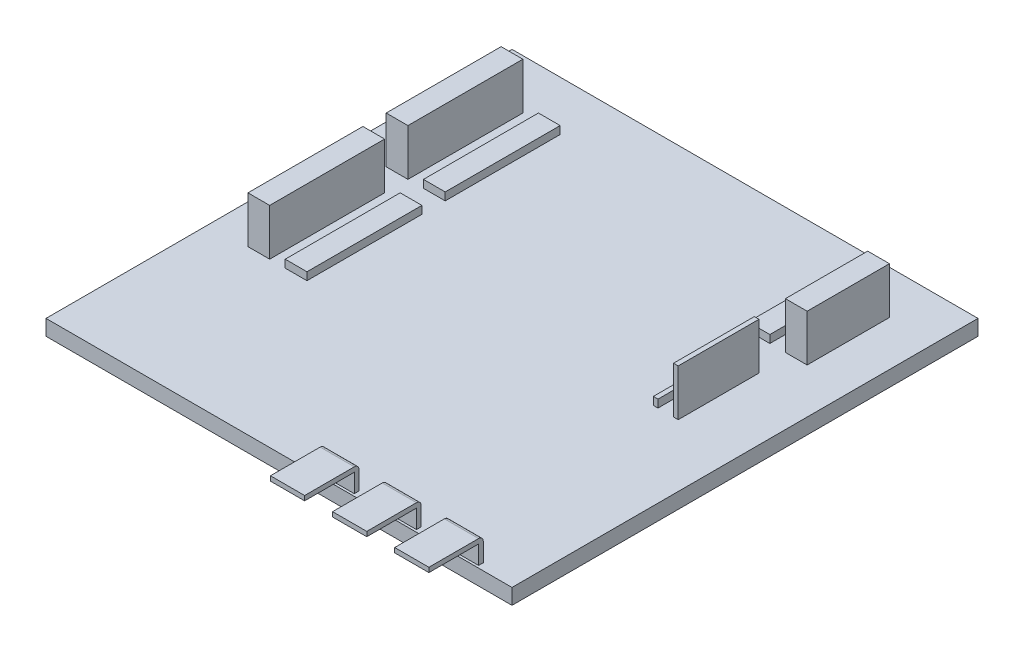
SolidWorks part; units mm, degrees
material "Custom Plastic"
ref_plane "Front Plane" through (0, 0, 0) normal (0, 0, 1) x (1, 0, 0)
ref_plane "Top Plane" through (0, 0, 0) normal (0, 1, 0) x (1, 0, 0)
ref_plane "Right Plane" through (0, 0, 0) normal (1, 0, 0) x (0, 0, -1)
sketch "Sketch1" plane through (0, 0, 0) normal (0, 1, 0) x (1, 0, 0)
  line L1 (38.1, -38.1) -> (-38.1, -38.1)
  line L2 (38.1, -38.1) -> (38.1, 38.1)
  line L3 (38.1, 38.1) -> (-38.1, 38.1)
  line L4 (-38.1, -38.1) -> (-38.1, 38.1)
  line L5 (38.1, -38.1) -> (-38.1, 38.1) construction
  line L6 (38.1, 38.1) -> (-38.1, -38.1) construction
  point P0 (0, 0)
extrude "Extrude1" add sketch "Sketch1" along normal blind 2.54
sketch "Sketch2" plane through (0, 2.54, 0) normal (0, 1, 0) x (-1, 0, 0)
  line L0 (-38.1, -38.1) -> (-38.1, -30.988) construction
  line L1 (-38.1, 38.1) -> (-38.1, -38.1) construction
  line L2 (-38.1, -30.988) -> (-24.638, -30.988) construction
  line L3 (-24.638, -17.526) -> (-24.638, -12.446) construction
  line L4 (-24.638, -30.988) -> (-21.082, -30.988)
  line L5 (-24.638, -30.988) -> (-24.638, -17.526)
  line L6 (-24.638, -17.526) -> (-21.082, -17.526)
  line L7 (-21.082, -30.988) -> (-21.082, -17.526)
  line L8 (38.1, -38.1) -> (25.654, -38.1) construction
  line L9 (-24.638, -12.446) -> (-23.876, -12.446)
  line L10 (-24.638, -12.446) -> (-24.638, 0.762)
  line L11 (-24.638, 0.762) -> (-23.876, 0.762)
  line L12 (-23.876, -12.446) -> (-23.876, 0.762)
  line L13 (-38.1, -38.1) -> (38.1, -38.1) construction
  line L14 (25.654, -38.1) -> (25.654, -29.972) construction
  line L15 (25.654, -11.176) -> (25.654, -7.366) construction
  line L16 (25.654, -29.972) -> (22.098, -29.972)
  line L17 (25.654, -29.972) -> (25.654, -11.176)
  line L18 (25.654, -11.176) -> (22.098, -11.176)
  line L19 (22.098, -29.972) -> (22.098, -11.176)
  line L20 (25.654, -29.972) -> (28.194, -29.972) construction
  line L21 (25.654, -7.366) -> (22.098, -7.366)
  line L22 (25.654, -7.366) -> (25.654, 11.43)
  line L23 (25.654, 11.43) -> (22.098, 11.43)
  line L24 (22.098, -7.366) -> (22.098, 11.43)
  line L25 (-24.638, -30.988) -> (-27.178, -30.988) construction
  line L26 (28.194, -29.972) -> (31.75, -29.972)
  line L27 (28.194, -29.972) -> (28.194, -11.176)
  line L28 (28.194, -11.176) -> (31.75, -11.176)
  line L29 (31.75, -29.972) -> (31.75, -11.176)
  line L30 (28.194, -7.366) -> (31.75, -7.366)
  line L31 (28.194, -7.366) -> (28.194, 11.43)
  line L32 (28.194, 11.43) -> (31.75, 11.43)
  line L33 (31.75, -7.366) -> (31.75, 11.43)
  line L34 (-24.638, -12.446) -> (-27.178, -12.446) construction
  line L35 (-27.178, -30.988) -> (-30.734, -30.988)
  line L36 (-27.178, -30.988) -> (-27.178, -17.526)
  line L37 (-27.178, -17.526) -> (-30.734, -17.526)
  line L38 (-30.734, -30.988) -> (-30.734, -17.526)
  line L39 (-27.178, -12.446) -> (-27.94, -12.446) construction
  line L40 (22.098, -29.972) -> (-21.082, -29.972) construction
  line L41 (-27.178, -12.446) -> (-27.94, -12.446)
  line L42 (-27.178, -12.446) -> (-27.178, 0.762)
  line L43 (-27.178, 0.762) -> (-27.94, 0.762)
  line L44 (-27.94, -12.446) -> (-27.94, 0.762)
  line L45 (25.654, -7.366) -> (28.194, -7.366) construction
extrude "Extrude2" add sketch "Sketch2" along normal blind 1.27 and the other way blind 10.1601
sketch "Sketch3" plane through (0, 2.54, 0) normal (0, 1, 0) x (-1, 0, 0)
  line L0 (38.1, 38.1) -> (38.1, 36.83) construction
  line L1 (38.1, -38.1) -> (38.1, 38.1) construction
  line L2 (38.1, 38.1) -> (-6.35, 38.1) construction
  line L3 (38.1, 38.1) -> (-38.1, 38.1) construction
  line L4 (-6.35, 38.1) -> (-6.35, 37.719) construction
  line L5 (-6.35, 38.1) -> (-4.318, 38.1) construction
  line L10 (-11.938, 36.957) -> (-11.938, 37.719)
  line L11 (-6.35, 37.719) -> (-11.938, 37.719)
  line L12 (-6.35, 36.957) -> (-6.35, 37.719)
  line L13 (-6.35, 36.957) -> (-11.938, 36.957)
extrude "Extrude3" add sketch "Sketch3" along normal blind 3.048
pattern_linear "LPattern1" count 3 spacing 10.16 along (1, 0, 0) of "Extrude3"
sketch "Sketch8" plane through (0, 5.588, 0) normal (0, 1, 0) x (1, 0, 0)
  line L1 (6.35, -36.957) -> (11.938, -36.957)
  line L2 (6.35, -36.957) -> (6.35, -37.719)
  line L3 (6.35, -37.719) -> (11.938, -37.719)
  line L4 (11.938, -36.957) -> (11.938, -37.719)
  line L5 (16.51, -36.957) -> (22.098, -36.957)
  line L6 (16.51, -36.957) -> (16.51, -37.719)
  line L7 (16.51, -37.719) -> (22.098, -37.719)
  line L8 (22.098, -36.957) -> (22.098, -37.719)
  line L9 (26.67, -36.957) -> (32.258, -36.957)
  line L10 (26.67, -36.957) -> (26.67, -37.719)
  line L11 (26.67, -37.719) -> (32.258, -37.719)
  line L12 (32.258, -36.957) -> (32.258, -37.719)
revolve "Revolve3" add sketch "Sketch8" angle 90 about L3
sketch "Sketch9" plane through (0, 0, 37.719) normal (0, 0, 1) x (1, 0, 0)
  line L1 (6.35, 6.35) -> (11.938, 6.35)
  line L2 (6.35, 6.35) -> (6.35, 5.588)
  line L3 (6.35, 5.588) -> (11.938, 5.588)
  line L4 (11.938, 6.35) -> (11.938, 5.588)
extrude "Extrude5" add sketch "Sketch9" along normal blind 8.128
pattern_linear "LPattern2" count 3 spacing 10.16 along (1, 0, 0) of "Extrude5"
sketch "Sketch11" plane through (0, 3.81, 0) normal (0, 1, 0) x (1, 0, 0)
  line L1 (-31.75, 29.972) -> (-28.194, 29.972)
  line L2 (-31.75, 29.972) -> (-31.75, 11.176)
  line L3 (-31.75, 11.176) -> (-28.194, 11.176)
  line L4 (-28.194, 29.972) -> (-28.194, 11.176)
  line L5 (-28.194, 7.366) -> (-31.75, 7.366)
  line L6 (-28.194, 7.366) -> (-28.194, -11.43)
  line L7 (-28.194, -11.43) -> (-31.75, -11.43)
  line L8 (-31.75, 7.366) -> (-31.75, -11.43)
  line L9 (27.178, -0.762) -> (27.94, -0.762)
  line L10 (27.178, -0.762) -> (27.178, 12.446)
  line L11 (27.178, 12.446) -> (27.94, 12.446)
  line L12 (27.94, -0.762) -> (27.94, 12.446)
  line L13 (27.178, 17.526) -> (30.734, 17.526)
  line L14 (27.178, 17.526) -> (27.178, 30.988)
  line L15 (27.178, 30.988) -> (30.734, 30.988)
  line L16 (30.734, 17.526) -> (30.734, 30.988)
extrude "Extrude6" add sketch "Sketch11" along normal blind 6.35
sketch "Sketch12" plane through (0, -7.6201, 0) normal (0, -1, 0) x (1, 0, 0)
  line L1 (-31.75, -29.972) -> (-28.194, -29.972)
  line L2 (-31.75, -29.972) -> (-31.75, -11.176)
  line L3 (-31.75, -11.176) -> (-28.194, -11.176)
  line L4 (-28.194, -29.972) -> (-28.194, -11.176)
  line L5 (-31.75, -7.366) -> (-28.194, -7.366)
  line L6 (-31.75, -7.366) -> (-31.75, 11.43)
  line L7 (-31.75, 11.43) -> (-28.194, 11.43)
  line L8 (-28.194, -7.366) -> (-28.194, 11.43)
  line L9 (27.178, -30.988) -> (30.734, -30.988)
  line L10 (27.178, -30.988) -> (27.178, -17.526)
  line L11 (27.178, -17.526) -> (30.734, -17.526)
  line L12 (30.734, -30.988) -> (30.734, -17.526)
  line L13 (27.178, -12.446) -> (27.94, -12.446)
  line L14 (27.178, -12.446) -> (27.178, 0.762)
  line L15 (27.178, 0.762) -> (27.94, 0.762)
  line L16 (27.94, -12.446) -> (27.94, 0.762)
extrude "Extrude7" cut sketch "Sketch12" against normal up to surface (7.6201 mm away) up to face at (27.559, 0, -5.842)
